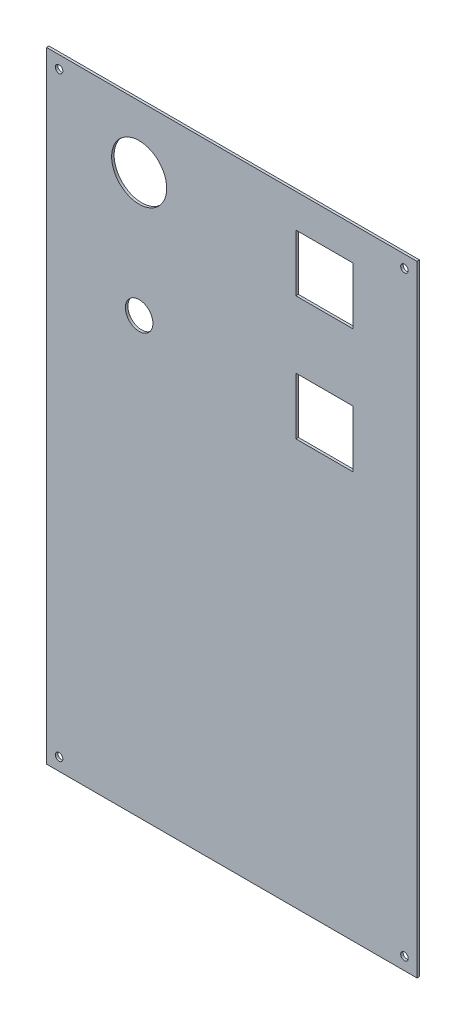
SolidWorks part; units mm, degrees
material "Plain Carbon Steel"
ref_plane "Front Plane" through (0, 0, 0) normal (0, 0, 1) x (1, 0, 0)
ref_plane "Top Plane" through (0, 0, 0) normal (0, 1, 0) x (1, 0, 0)
ref_plane "Right Plane" through (0, 0, 0) normal (1, 0, 0) x (0, 0, -1)
sketch "Sketch1" plane through (0, 0, 0) normal (0, 0, 1) x (1, 0, 0)
  line L0 (148, 149) -> (-148, 149) construction
  line L1 (148, 248) -> (-148, 248)
  line L2 (148, 248) -> (148, -248)
  line L3 (148, -248) -> (-148, -248)
  line L4 (-148, 248) -> (-148, -248)
  line L5 (148, 248) -> (0, 149) construction
  line L6 (0, 248) -> (0, 50) construction
  line L7 (148, 50) -> (-148, 50) construction
  line L8 (0, 149) -> (148, 50) construction
  line L9 (-148, 50) -> (0, 149) construction
  line L10 (-148, 248) -> (0, 149) construction
  line L11 (-148, 248) -> (148, 248) construction
  line L12 (138, 238) -> (-138, 238) construction
  line L13 (51.25, 221.25) -> (96.75, 221.25)
  line L14 (51.25, 221.25) -> (51.25, 175.75)
  line L15 (51.25, 175.75) -> (96.75, 175.75)
  line L16 (96.75, 221.25) -> (96.75, 175.75)
  line L17 (51.25, 221.25) -> (96.75, 175.75) construction
  line L18 (51.25, 175.75) -> (96.75, 221.25) construction
  line L19 (51.25, 76.75) -> (96.75, 76.75)
  line L20 (51.25, 76.75) -> (51.25, 122.25)
  line L21 (51.25, 122.25) -> (96.75, 122.25)
  line L22 (96.75, 76.75) -> (96.75, 122.25)
  line L23 (51.25, 76.75) -> (96.75, 122.25) construction
  line L24 (51.25, 122.25) -> (96.75, 76.75) construction
  line L25 (-138, 238) -> (-138, -238) construction
  line L26 (138, -238) -> (-138, -238) construction
  line L27 (138, 238) -> (138, -238) construction
  circle A0 centre (-74, 99.5) radius 11
  circle A1 centre (-74, 198.5) radius 22
  circle A2 centre (-138, 238) radius 3
  circle A3 centre (138, 238) radius 3
  circle A4 centre (-138, -238) radius 3
  circle A5 centre (138, -238) radius 3
  point P0 (0, 0)
  point P12 (74, 198.5)
  point P19 (74, 99.5)
  dimension "D9" = 10
  dimension "D1" = 296
  dimension "D2" = 496
  dimension "D7" = 45.5
  dimension "D5" = 45.5
  dimension "D6" = 45.5
  dimension "D8" = 45.5
  dimension "D3" = 99
  dimension "D4" = 99
extrude "Boss-Extrude1" add sketch "Sketch1" along normal blind 2
